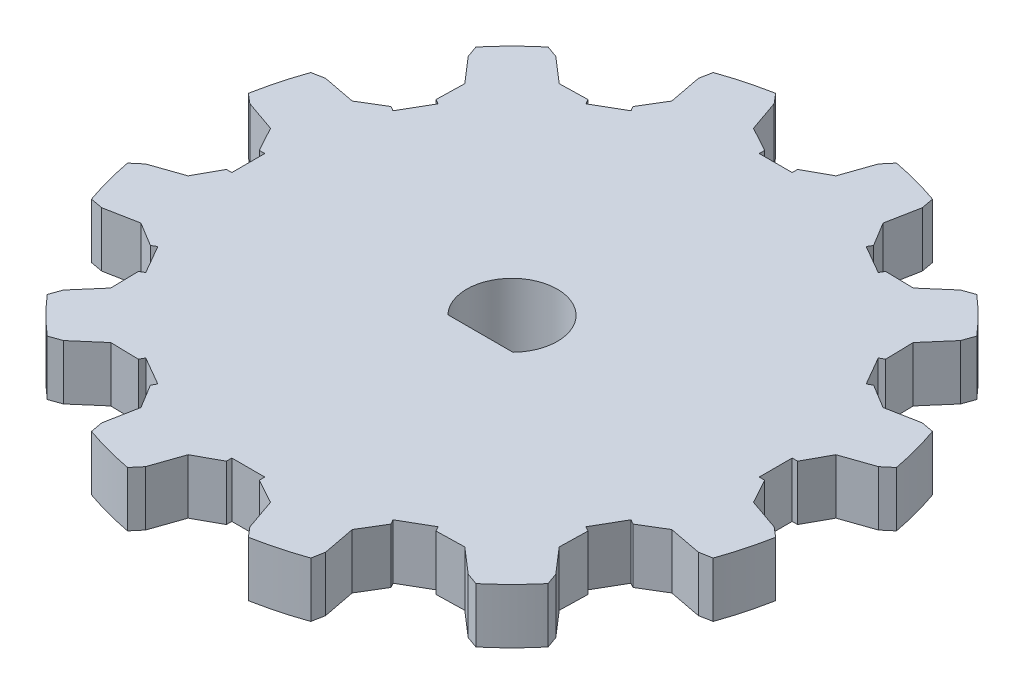
SolidWorks part; units mm, degrees
ref_plane "Front Plane" through (0, 0, 0) normal (0, 0, 1) x (1, 0, 0)
ref_plane "Top Plane" through (0, 0, 0) normal (0, 1, 0) x (1, 0, 0)
ref_plane "Right Plane" through (0, 0, 0) normal (1, 0, 0) x (0, 0, -1)
sketch "Sketch1" plane through (0, 0, 0) normal (0, 1, 0) x (1, 0, 0)
  line L0 (0, -1000) -> (0, 49000) construction
  line L1 (-3.75, 25.7281) -> (-4.75, 28.6083)
  line L2 (3.75, 25.7281) -> (4.75, 28.6083)
  line L3 (-3.75, 25.7281) -> (-1.5, 24.4948)
  line L4 (1.5, 24) -> (-1.5, 24)
  line L8 (-1.5, 24) -> (-1.5, 24.4948)
  line L9 (1.5, 24) -> (1.5, 24.4948)
  line L10 (3.75, 25.7281) -> (1.5, 24.4948)
  line L11 (4.75, 28.6083) -> (5.5, 29.4915)
  line L12 (-4.75, 28.6083) -> (-5.5, 29.4915)
  line L13 (18.4178, 22.4006) -> (19.5089, 22.7904)
  line L14 (16.1117, 20.4062) -> (18.4178, 22.4006)
  line L15 (16.1117, 20.4062) -> (13.5464, 20.4631)
  line L16 (13.299, 20.0346) -> (13.5464, 20.4631)
  line L17 (13.299, 20.0346) -> (10.701, 21.5346)
  line L18 (10.701, 21.5346) -> (10.9484, 21.9631)
  line L19 (9.6165, 24.1562) -> (10.9484, 21.9631)
  line L20 (9.6165, 24.1562) -> (10.1906, 27.1506)
  line L21 (10.1906, 27.1506) -> (9.9826, 28.2904)
  line L22 (27.1506, 10.1906) -> (28.2904, 9.9826)
  line L23 (24.1562, 9.6165) -> (27.1506, 10.1906)
  line L24 (24.1562, 9.6165) -> (21.9631, 10.9484)
  line L25 (21.5346, 10.701) -> (21.9631, 10.9484)
  line L26 (21.5346, 10.701) -> (20.0346, 13.299)
  line L27 (20.0346, 13.299) -> (20.4631, 13.5464)
  line L28 (20.4062, 16.1117) -> (20.4631, 13.5464)
  line L29 (20.4062, 16.1117) -> (22.4006, 18.4178)
  line L30 (22.4006, 18.4178) -> (22.7904, 19.5089)
  line L31 (28.6083, -4.75) -> (29.4915, -5.5)
  line L32 (25.7281, -3.75) -> (28.6083, -4.75)
  line L33 (25.7281, -3.75) -> (24.4948, -1.5)
  line L34 (24, -1.5) -> (24.4948, -1.5)
  line L35 (24, -1.5) -> (24, 1.5)
  line L36 (24, 1.5) -> (24.4948, 1.5)
  line L37 (25.7281, 3.75) -> (24.4948, 1.5)
  line L38 (25.7281, 3.75) -> (28.6083, 4.75)
  line L39 (28.6083, 4.75) -> (29.4915, 5.5)
  line L40 (22.4006, -18.4178) -> (22.7904, -19.5089)
  line L41 (20.4062, -16.1117) -> (22.4006, -18.4178)
  line L42 (20.4062, -16.1117) -> (20.4631, -13.5464)
  line L43 (20.0346, -13.299) -> (20.4631, -13.5464)
  line L44 (20.0346, -13.299) -> (21.5346, -10.701)
  line L45 (21.5346, -10.701) -> (21.9631, -10.9484)
  line L46 (24.1562, -9.6165) -> (21.9631, -10.9484)
  line L47 (24.1562, -9.6165) -> (27.1506, -10.1906)
  line L48 (27.1506, -10.1906) -> (28.2904, -9.9826)
  line L49 (10.1906, -27.1506) -> (9.9826, -28.2904)
  line L50 (9.6165, -24.1562) -> (10.1906, -27.1506)
  line L51 (9.6165, -24.1562) -> (10.9484, -21.9631)
  line L52 (10.701, -21.5346) -> (10.9484, -21.9631)
  line L53 (10.701, -21.5346) -> (13.299, -20.0346)
  line L54 (13.299, -20.0346) -> (13.5464, -20.4631)
  line L55 (16.1117, -20.4062) -> (13.5464, -20.4631)
  line L56 (16.1117, -20.4062) -> (18.4178, -22.4006)
  line L57 (18.4178, -22.4006) -> (19.5089, -22.7904)
  line L58 (-4.75, -28.6083) -> (-5.5, -29.4915)
  line L59 (-3.75, -25.7281) -> (-4.75, -28.6083)
  line L60 (-3.75, -25.7281) -> (-1.5, -24.4948)
  line L61 (-1.5, -24) -> (-1.5, -24.4948)
  line L62 (-1.5, -24) -> (1.5, -24)
  line L63 (1.5, -24) -> (1.5, -24.4948)
  line L64 (3.75, -25.7281) -> (1.5, -24.4948)
  line L65 (3.75, -25.7281) -> (4.75, -28.6083)
  line L66 (4.75, -28.6083) -> (5.5, -29.4915)
  line L67 (-18.4178, -22.4006) -> (-19.5089, -22.7904)
  line L68 (-16.1117, -20.4062) -> (-18.4178, -22.4006)
  line L69 (-16.1117, -20.4062) -> (-13.5464, -20.4631)
  line L70 (-13.299, -20.0346) -> (-13.5464, -20.4631)
  line L71 (-13.299, -20.0346) -> (-10.701, -21.5346)
  line L72 (-10.701, -21.5346) -> (-10.9484, -21.9631)
  line L73 (-9.6165, -24.1562) -> (-10.9484, -21.9631)
  line L74 (-9.6165, -24.1562) -> (-10.1906, -27.1506)
  line L75 (-10.1906, -27.1506) -> (-9.9826, -28.2904)
  line L76 (-27.1506, -10.1906) -> (-28.2904, -9.9826)
  line L77 (-24.1562, -9.6165) -> (-27.1506, -10.1906)
  line L78 (-24.1562, -9.6165) -> (-21.9631, -10.9484)
  line L79 (-21.5346, -10.701) -> (-21.9631, -10.9484)
  line L80 (-21.5346, -10.701) -> (-20.0346, -13.299)
  line L81 (-20.0346, -13.299) -> (-20.4631, -13.5464)
  line L82 (-20.4062, -16.1117) -> (-20.4631, -13.5464)
  line L83 (-20.4062, -16.1117) -> (-22.4006, -18.4178)
  line L84 (-22.4006, -18.4178) -> (-22.7904, -19.5089)
  line L85 (-28.6083, 4.75) -> (-29.4915, 5.5)
  line L86 (-25.7281, 3.75) -> (-28.6083, 4.75)
  line L87 (-25.7281, 3.75) -> (-24.4948, 1.5)
  line L88 (-24, 1.5) -> (-24.4948, 1.5)
  line L89 (-24, 1.5) -> (-24, -1.5)
  line L90 (-24, -1.5) -> (-24.4948, -1.5)
  line L91 (-25.7281, -3.75) -> (-24.4948, -1.5)
  line L92 (-25.7281, -3.75) -> (-28.6083, -4.75)
  line L93 (-28.6083, -4.75) -> (-29.4915, -5.5)
  line L94 (-22.4006, 18.4178) -> (-22.7904, 19.5089)
  line L95 (-20.4062, 16.1117) -> (-22.4006, 18.4178)
  line L96 (-20.4062, 16.1117) -> (-20.4631, 13.5464)
  line L97 (-20.0346, 13.299) -> (-20.4631, 13.5464)
  line L98 (-20.0346, 13.299) -> (-21.5346, 10.701)
  line L99 (-21.5346, 10.701) -> (-21.9631, 10.9484)
  line L100 (-24.1562, 9.6165) -> (-21.9631, 10.9484)
  line L101 (-24.1562, 9.6165) -> (-27.1506, 10.1906)
  line L102 (-27.1506, 10.1906) -> (-28.2904, 9.9826)
  line L103 (-10.1906, 27.1506) -> (-9.9826, 28.2904)
  line L104 (-9.6165, 24.1562) -> (-10.1906, 27.1506)
  line L105 (-9.6165, 24.1562) -> (-10.9484, 21.9631)
  line L106 (-10.701, 21.5346) -> (-10.9484, 21.9631)
  line L107 (-10.701, 21.5346) -> (-13.299, 20.0346)
  line L108 (-13.299, 20.0346) -> (-13.5464, 20.4631)
  line L109 (-16.1117, 20.4062) -> (-13.5464, 20.4631)
  line L110 (-16.1117, 20.4062) -> (-18.4178, 22.4006)
  line L111 (-18.4178, 22.4006) -> (-19.5089, 22.7904)
  circle A0 centre (0, 0) radius 25 construction
  circle A1 centre (0, 0) radius 26 construction
  circle A2 centre (0, 0) radius 30 construction
  circle A3 centre (0, 0) radius 29 construction
  arc A4 (5.5, 29.4915) -> (8, 28.9137) centre (0, 0) cw
  arc A5 (-5.5, 29.4915) -> (-8, 28.9137) centre (0, 0) ccw
  arc A6 (19.5089, 22.7904) -> (21.385, 21.04) centre (0, 0) cw
  arc A7 (9.9826, 28.2904) -> (7.5286, 29.04) centre (0, 0) ccw
  arc A8 (28.2904, 9.9826) -> (29.04, 7.5286) centre (0, 0) cw
  arc A9 (22.7904, 19.5089) -> (21.04, 21.385) centre (0, 0) ccw
  arc A10 (29.4915, -5.5) -> (28.9137, -8) centre (0, 0) cw
  arc A11 (29.4915, 5.5) -> (28.9137, 8) centre (0, 0) ccw
  arc A12 (22.7904, -19.5089) -> (21.04, -21.385) centre (0, 0) cw
  arc A13 (28.2904, -9.9826) -> (29.04, -7.5286) centre (0, 0) ccw
  arc A14 (9.9826, -28.2904) -> (7.5286, -29.04) centre (0, 0) cw
  arc A15 (19.5089, -22.7904) -> (21.385, -21.04) centre (0, 0) ccw
  arc A16 (-5.5, -29.4915) -> (-8, -28.9137) centre (0, 0) cw
  arc A17 (5.5, -29.4915) -> (8, -28.9137) centre (0, 0) ccw
  arc A18 (-19.5089, -22.7904) -> (-21.385, -21.04) centre (0, 0) cw
  arc A19 (-9.9826, -28.2904) -> (-7.5286, -29.04) centre (0, 0) ccw
  arc A20 (-28.2904, -9.9826) -> (-29.04, -7.5286) centre (0, 0) cw
  arc A21 (-22.7904, -19.5089) -> (-21.04, -21.385) centre (0, 0) ccw
  arc A22 (-29.4915, 5.5) -> (-28.9137, 8) centre (0, 0) cw
  arc A23 (-29.4915, -5.5) -> (-28.9137, -8) centre (0, 0) ccw
  arc A24 (-22.7904, 19.5089) -> (-21.04, 21.385) centre (0, 0) cw
  arc A25 (-28.2904, 9.9826) -> (-29.04, 7.5286) centre (0, 0) ccw
  arc A26 (-9.9826, 28.2904) -> (-7.5286, 29.04) centre (0, 0) cw
  arc A27 (-19.5089, 22.7904) -> (-21.385, 21.04) centre (0, 0) ccw
  point P12 (0, 25)
  point P156 (0, 0)
  dimension "D1" = 50
  dimension "D2" = 52
  dimension "D3" = 60
  dimension "D4" = 58
  dimension "D5" = 3.75
  dimension "D6" = 4.75
  dimension "D8" = 4.75
  dimension "D10" = 3
  dimension "D7" = 3.75
  dimension "D9" = 25
  dimension "D11" = 1.5
  dimension "D12" = 24
  dimension "D13" = 118.729
  dimension "D14" = 118.729
  dimension "D15" = 5.5
  dimension "D16" = 5.5
  dimension "D17" = 8
  dimension "D18" = 8
  dimension "D19" = 12
extrude "Boss-Extrude1" add sketch "Sketch1" along normal blind 5 contours L111 A27 A24 L94 L95 L96 L97 L98 L99 L100 L101 L102 A25 A22 L85 L86 L87 L88 L89 L90 L91 L92 L93 A23 A20 L76 L77 L78 L79 L80 L81 L82 L83 L84 A21 A18 L67 L68 L69 L70 L71 L72 L73 L74 L75 A19 A16
sketch "Sketch5" plane through (0, 0, 0) normal (0, -1, 0) x (1, 0, 0)
  circle A0 centre (0, 0) radius 17.5
  dimension "D1" = 35
extrude "Boss-Extrude2" add sketch "Sketch5" along normal blind 2.5
sketch "Sketch6" plane through (0, -2.5, 0) normal (0, -1, 0) x (1, 0, 0)
  line L1 (2.958, 5.375) -> (-2.958, 5.375)
  line L2 (2.958, 5.375) -> (2.958, 2.875)
  line L3 (2.958, 2.875) -> (-2.958, 2.875)
  line L4 (-2.958, 5.375) -> (-2.958, 2.875)
  line L5 (2.958, 5.375) -> (-2.958, 2.875) construction
  line L6 (2.958, 2.875) -> (-2.958, 5.375) construction
  circle A0 centre (0, 0) radius 4.125
  point P3 (0, 4.125)
  dimension "D1" = 8.25
  dimension "D2" = 2.5
extrude "Cut-Extrude2" cut sketch "Sketch6" against normal through all both and the other way through all contours L3 A0
